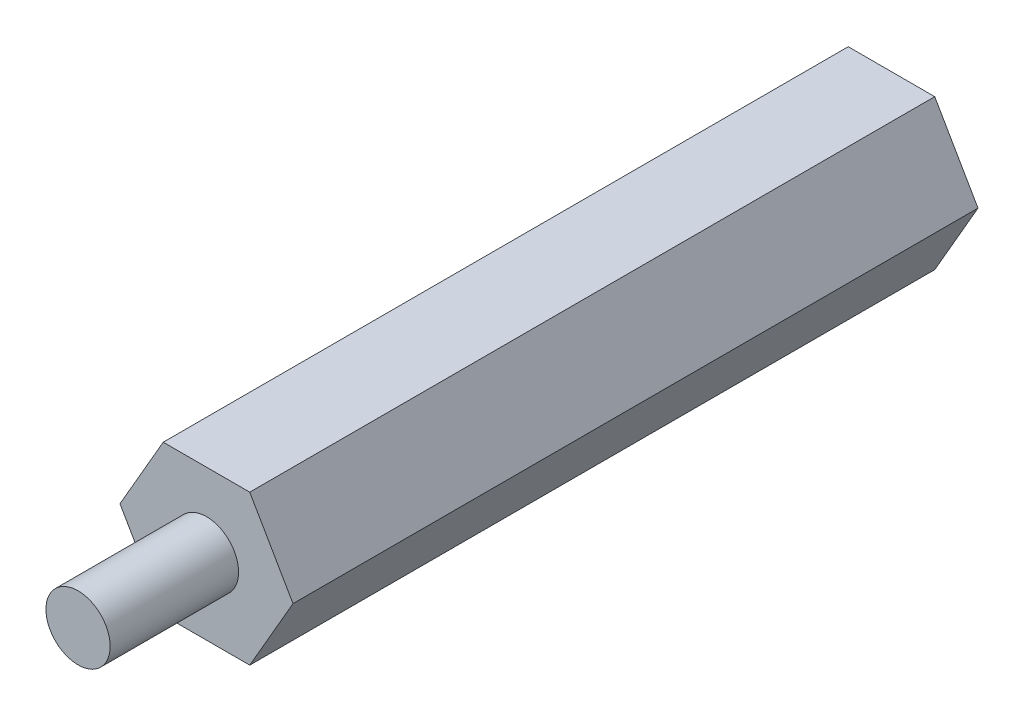
SolidWorks part; units mm, degrees
ref_plane "前视基准面" through (0, 0, 0) normal (0, 0, 1) x (1, 0, 0)
ref_plane "上视基准面" through (0, 0, 0) normal (0, 1, 0) x (1, 0, 0)
ref_plane "右视基准面" through (0, 0, 0) normal (1, 0, 0) x (0, 0, -1)
sketch "草图1" plane through (0, 0, 0) normal (0, 0, 1) x (1, 0, 0)
  line L1 (4.0415, 0) -> (2.0207, 3.5)
  line L2 (2.0207, 3.5) -> (-2.0207, 3.5)
  line L3 (-2.0207, 3.5) -> (-4.0415, 0)
  line L4 (-4.0415, 0) -> (-2.0207, -3.5)
  line L5 (-2.0207, -3.5) -> (2.0207, -3.5)
  line L6 (2.0207, -3.5) -> (4.0415, 0)
  circle A0 centre (0, 0) radius 3.5 construction
  dimension "D1" = 7
extrude "凸台-拉伸1" add sketch "草图1" along normal blind 32
sketch "草图2" plane through (0, 0, 32) normal (0, 0, 1) x (1, 0, 0)
  circle A0 centre (0, 0) radius 1.5
  dimension "D1" = 3
extrude "凸台-拉伸2" add sketch "草图2" along normal blind 6
cosmetic thread "装饰螺纹线1" parameters "D1"=2.4, "D2"=2.459
hole_wizard "M3 螺纹孔1" positions "草图3" profile "草图4" tap size "M3" standard "ISO"
sketch "草图3" plane through (0, 0, 0) normal (0, 0, -1) x (-1, 0, 0)
  point P0 (0, 0)
cosmetic thread "孔螺蚊线1"
sketch "草图4" plane through (0, 0, 0) normal (1, 0, 0) x (0, 1, 0)
  line L0 (0, 0) -> (0, 4.6511)
  line L1 (0, 4.6511) -> (1.25, 3.9)
  line L2 (1.25, 3.9) -> (1.25, 0)
  line L5 (1.25, 0) -> (0, 0)
  line L10 (0, 4.6511) -> (-1.25, 3.9) construction
  line L11 (0, -6.35) -> (0, 107.95) construction
  dimension "螺纹孔钻头直径" = 2.5
  dimension "螺纹孔钻头深度" = 3.9
  dimension "导头角度" = 118
